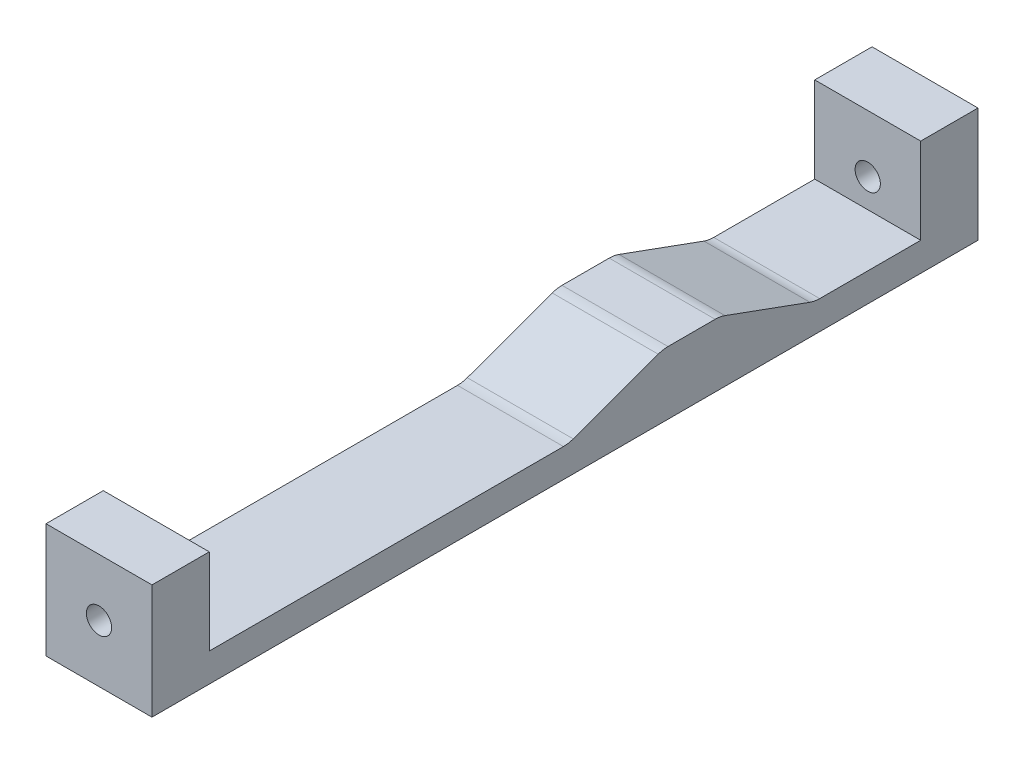
SolidWorks part; units mm, degrees
ref_plane "Front Plane" through (0, 0, 0) normal (0, 0, 1) x (1, 0, 0)
ref_plane "Top Plane" through (0, 0, 0) normal (0, 1, 0) x (1, 0, 0)
ref_plane "Right Plane" through (0, 0, 0) normal (1, 0, 0) x (0, 0, -1)
sketch "Sketch1" plane through (0, 0, 0) normal (0, 1, 0) x (1, 0, 0)
  line L1 (-5.8738, -45.7835) -> (5.8738, -45.7835)
  line L2 (-5.8738, -45.7835) -> (-5.8738, 45.7835)
  line L3 (-5.8738, 45.7835) -> (5.8738, 45.7835)
  line L4 (5.8738, -45.7835) -> (5.8738, 45.7835)
  line L5 (-5.8738, -45.7835) -> (5.8738, 45.7835) construction
  line L6 (-5.8738, 45.7835) -> (5.8738, -45.7835) construction
  point P0 (0, 0)
  point P6 (0, 0)
  dimension "D1" = 11.7475
  dimension "D2" = 91.567
extrude "Boss-Extrude1" add sketch "Sketch1" along normal blind 3.175
sketch "Sketch4" plane through (0, 0, 45.7835) normal (0, 0, 1) x (1, 0, 0)
  circle A0 centre (0, 6.35) radius 1.4
  dimension "D1" = 2.8
  dimension "D2" = 6.35
sketch "Sketch5" plane through (0, 0, 45.7835) normal (0, 0, 1) x (1, 0, 0)
  line L1 (-5.8738, 3.175) -> (5.8738, 3.175)
  line L2 (-5.8738, 3.175) -> (-5.8738, 12.7)
  line L3 (-5.8738, 12.7) -> (5.8738, 12.7)
  line L4 (5.8738, 3.175) -> (5.8738, 12.7)
  dimension "D1" = 9.525
extrude "Boss-Extrude2" add sketch "Sketch5" against normal blind 6.35
mirror "Mirror1" about plane through (0, 0, 0) normal (0, 0, 1) of "Boss-Extrude2"
extrude "Cut-Extrude1" cut sketch "Sketch4" against normal through all
sketch "Sketch6" plane through (-5.8738, 0, 0) normal (-1, 0, 0) x (0, 0, 1)
  line L0 (-17.2085, 6.985) -> (-10.8585, 6.985)
  line L1 (-45.7835, 12.7) -> (-45.7835, 0) construction
  line L2 (-17.2085, 6.985) -> (-27.6764, 3.175)
  line L3 (-39.4335, 3.175) -> (39.4335, 3.175) construction
  line L4 (-27.6764, 3.175) -> (-0.3906, 3.175)
  line L5 (-0.3906, 3.175) -> (-10.8585, 6.985)
  point P2 (-14.0335, 6.985)
  dimension "D1" = 31.75
  dimension "D2" = 6.35
  dimension "D3" = 20
  dimension "D4" = 20
  dimension "D5" = 3.81
extrude "Boss-Extrude3" add sketch "Sketch6" against normal up to surface (11.7475 mm away) up to face at (5.8738, 7.1437, 0)
fillet "Fillet1" radius 3.175 4 edges at (0, 3.175, -0.3906) (0, 6.985, -10.8585) (0, 3.175, -27.6764) (0, 6.985, -17.2085)
equation "\"tighttol\" = 0.005in"
equation "\"normtol\" = 0.01in"
equation "\"loosetol\" = 0.02in"
equation "\"Fry height\"= 0.5in"
equation "\"Fry spacing\"= 0.5625in"
equation "\"Potato width\"= \"Fry spacing\" * 4"
equation "\"Potato length\"= 80mm"
equation "\"D1@Sketch1\"=\"Fry spacing\" - 5 * \"loosetol\""
equation "\"D2@Sketch1\"=3.625-\"loosetol\""
equation "\"D1@Sketch4\"=2.8mm"
